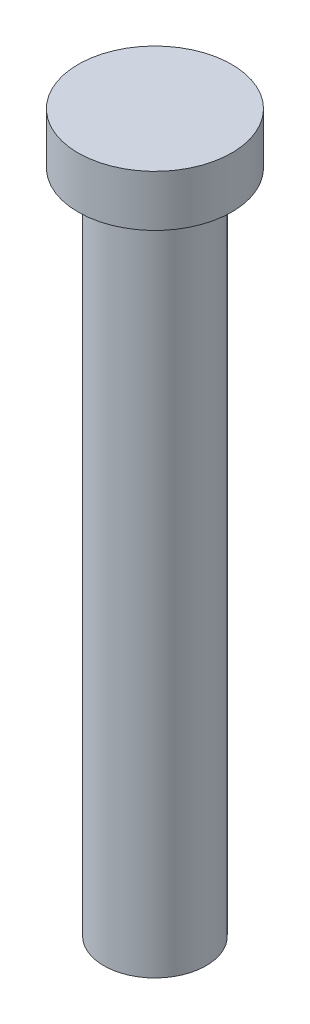
SolidWorks part; units mm, degrees
material "6061 Alloy"
ref_plane "Front Plane" through (0, 0, 0) normal (0, 0, 1) x (1, 0, 0)
ref_plane "Top Plane" through (0, 0, 0) normal (0, 1, 0) x (1, 0, 0)
ref_plane "Right Plane" through (0, 0, 0) normal (1, 0, 0) x (0, 0, -1)
sketch "Sketch1" plane through (0, 0, 0) normal (0, 1, 0) x (1, 0, 0)
  circle A0 centre (0, 0) radius 1.905
  dimension "D1" = 3.81
extrude "Boss-Extrude1" add sketch "Sketch1" along normal blind 1.27
sketch "Sketch2" plane through (0, 0, 0) normal (0, -1, 0) x (1, 0, 0)
  circle A0 centre (0, 0) radius 1.27
  dimension "D1" = 2.54
extrude "Boss-Extrude2" add sketch "Sketch2" along normal blind 16.51
